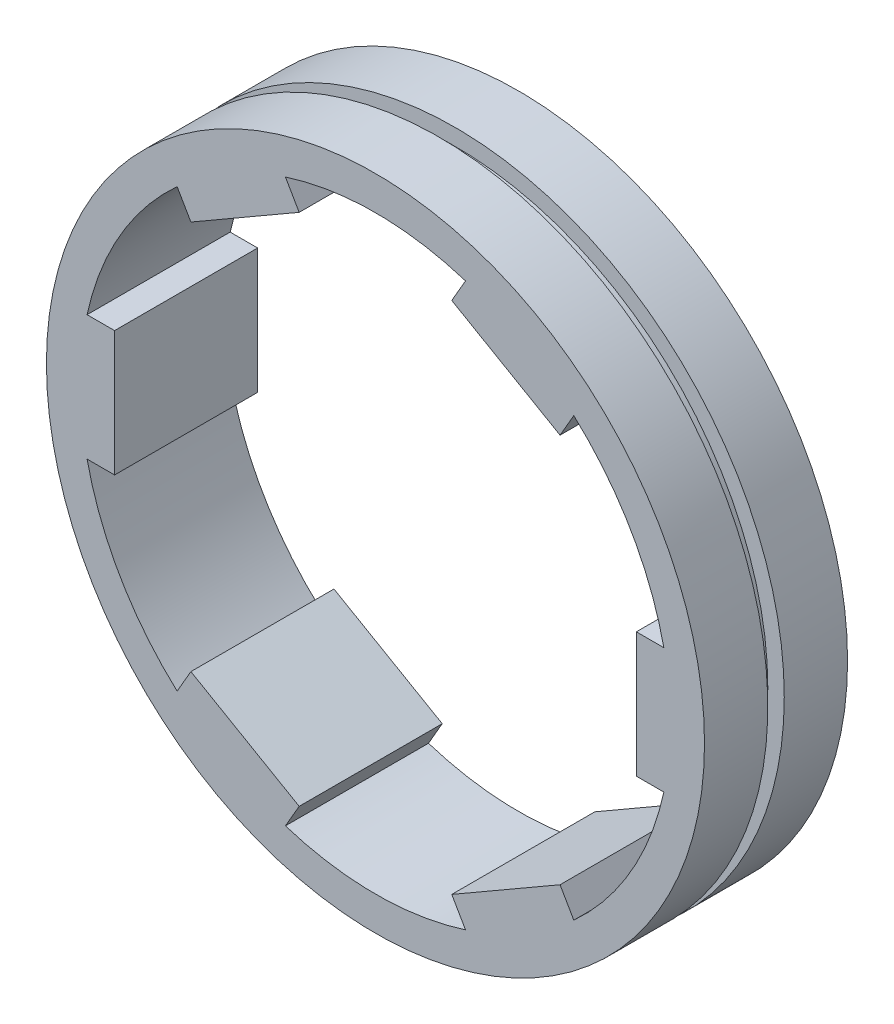
SolidWorks part; units mm, degrees
ref_plane "Front Plane" through (0, 0, 0) normal (0, 0, 1) x (1, 0, 0)
ref_plane "Top Plane" through (0, 0, 0) normal (0, 1, 0) x (1, 0, 0)
ref_plane "Right Plane" through (0, 0, 0) normal (1, 0, 0) x (0, 0, -1)
sketch "Sketch2" plane through (0, 0, 0) normal (0, 0, 1) x (1, 0, 0)
  circle A0 centre (0, 0) radius 20.625
  circle A1 centre (0, 0) radius 23
  dimension "D1" = 41.25
  dimension "D2" = 46
extrude "Boss-Extrude1" add sketch "Sketch2" along normal blind 10
sketch "Sketch3" plane through (0, 0, 0) normal (0, 0, 1) x (1, 0, 0)
  line L1 (-18.235, 4.37) -> (-20.765, 4.37)
  line L2 (-18.235, 4.37) -> (-18.235, -4.37)
  line L3 (-18.235, -4.37) -> (-20.765, -4.37)
  line L4 (-20.765, 4.37) -> (-20.765, -4.37)
  line L5 (-18.235, 4.37) -> (-20.765, -4.37) construction
  line L6 (-18.235, -4.37) -> (-20.765, 4.37) construction
  point P0 (-19.5, 0)
  dimension "D1" = 8.74
  dimension "D2" = 2.53
  dimension "D3" = 19.5
extrude "Boss-Extrude2" add sketch "Sketch3" along normal up to surface (10 mm away) from surface at 0 up to face at (23, 0, 10) starting at face at (23, 0, 0)
pattern_circular "CirPattern1" count 6 over 360 about axis through (0, 0, 0) along (0, 0, 1) of "Boss-Extrude2"
sketch "Sketch4" plane through (0, 0, 0) normal (1, 0, 0) x (0, 0, -1)
  line L0 (0, 23) -> (-10, 23) construction
  line L1 (-4.425, 24.15) -> (-5.575, 24.15)
  line L2 (-4.425, 24.15) -> (-4.425, 21.85)
  line L3 (-4.425, 21.85) -> (-5.575, 21.85)
  line L4 (-5.575, 24.15) -> (-5.575, 21.85)
  line L5 (-4.425, 24.15) -> (-5.575, 21.85) construction
  line L6 (-4.425, 21.85) -> (-5.575, 24.15) construction
  point P0 (-5, 23)
  dimension "D1" = 2.3
  dimension "D2" = 1.15
revolve "Cut-Revolve1" cut sketch "Sketch4" angle 360 about axis through (0, 0, 10) along (0, 0, -1)
